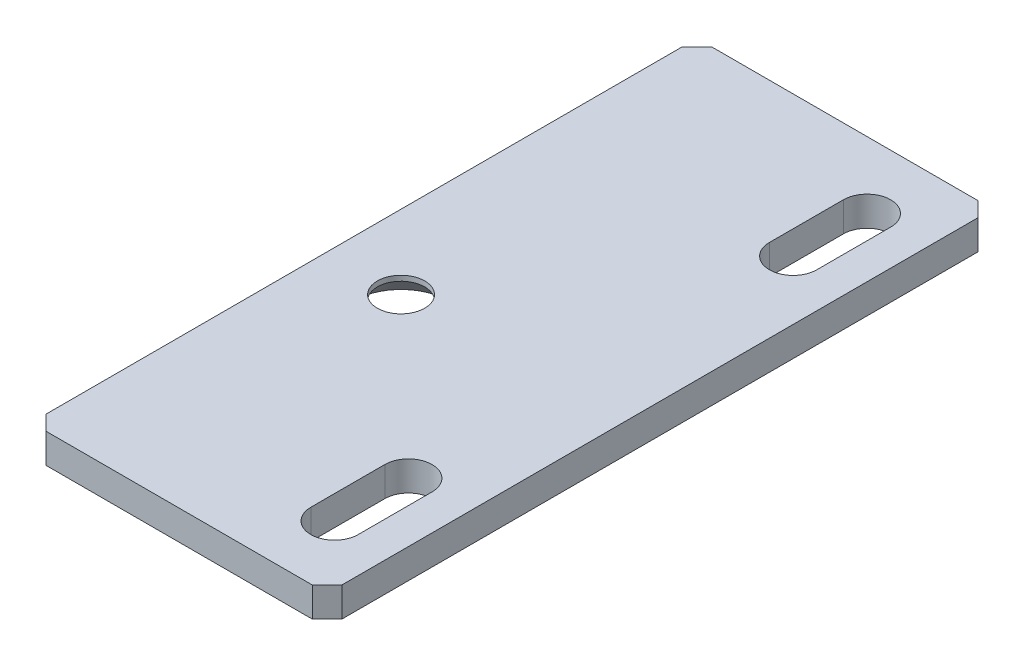
SolidWorks part; units mm, degrees
material "6061 Alloy"
ref_plane "Front Plane" through (0, 0, 0) normal (0, 0, 1) x (1, 0, 0)
ref_plane "Top Plane" through (0, 0, 0) normal (0, 1, 0) x (1, 0, 0)
ref_plane "Right Plane" through (0, 0, 0) normal (1, 0, 0) x (0, 0, -1)
sketch "Sketch1" plane through (0, 0, 0) normal (0, 1, 0) x (1, 0, 0)
  line L5 (10, -22.5) -> (-10, -22.5)
  line L6 (10, -22.5) -> (10, 22.5)
  line L7 (10, 22.5) -> (-10, 22.5)
  line L8 (-10, -22.5) -> (-10, 22.5)
  line L9 (10, -22.5) -> (-10, 22.5) construction
  line L10 (10, 22.5) -> (-10, -22.5) construction
  point P0 (0, 0)
  dimension "D3" = 20
  dimension "D4" = 45
extrude "BaseSheet" add sketch "Sketch1" along normal blind 2
sketch "Sketch6" plane through (0, 2, 0) normal (0, 1, 0) x (1, 0, 0)
  line L0 (6, 18) -> (6, 13) construction
  line L1 (7.6, 18) -> (7.6, 13)
  line L2 (4.4, 18) -> (4.4, 13)
  line L3 (6, -13) -> (6, -18) construction
  line L4 (7.6, -13) -> (7.6, -18)
  line L5 (4.4, -13) -> (4.4, -18)
  line L6 (0, 0) -> (-4.8321, 0) construction
  line L7 (10, -22.5) -> (10, 22.5) construction
  line L8 (10, 22.5) -> (-10, 22.5) construction
  arc A0 (7.6, 18) -> (4.4, 18) centre (6, 18) ccw
  arc A1 (4.4, 13) -> (7.6, 13) centre (6, 13) ccw
  arc A2 (7.6, -13) -> (4.4, -13) centre (6, -13) ccw
  arc A3 (4.4, -18) -> (7.6, -18) centre (6, -18) ccw
  point P3 (6, 15.5)
  point P8 (6, -15.5)
  dimension "D1" = 3.2
  dimension "D2" = 5
  dimension "D3" = 31
  dimension "D4" = 4
  dimension "D5" = 4.5
extrude "ScrewSlots" cut sketch "Sketch6" against normal through all
hole_wizard "PulleyHole" positions "Sketch4" profile "Sketch5" countersink size "M3" standard "ANSI Metric" end condition through all
sketch "Sketch4" plane through (0, 0, 0) normal (0, -1, 0) x (-1, 0, 0)
  line L2 (-10, -22.5) -> (-10, 22.5) construction
  line L4 (-10, 22.5) -> (10, 22.5) construction
  point P0 (5, -2.5)
  dimension "D1" = 25
  dimension "D2" = 15
sketch "Sketch5" plane through (-5, 0, 2.5) normal (1, 0, 0) x (0, 0, -1)
  line L0 (0, 0) -> (0, 2)
  line L1 (0, 2) -> (1.6, 2)
  line L2 (1.6, 2) -> (1.6, 1.65)
  line L3 (1.6, 1.65) -> (3.25, 0)
  line L5 (3.25, 0) -> (0, 0)
  line L6 (-1.6, 1.65) -> (-3.25, 0) construction
  line L11 (0, -6.35) -> (0, 107.95) construction
  dimension "Thru Hole Dia." = 3.2
  dimension "Thru Hole Depth" = 2
  dimension "Near C'Sink Dia." = 6.5
  dimension "Near C'Sink Angle" = 90
chamfer "Chamfer1x45" distance 1 angle 45 4 edges at (-10, 1, -22.5) (10, 1, -22.5) (10, 1, 22.5) (-10, 1, 22.5)
